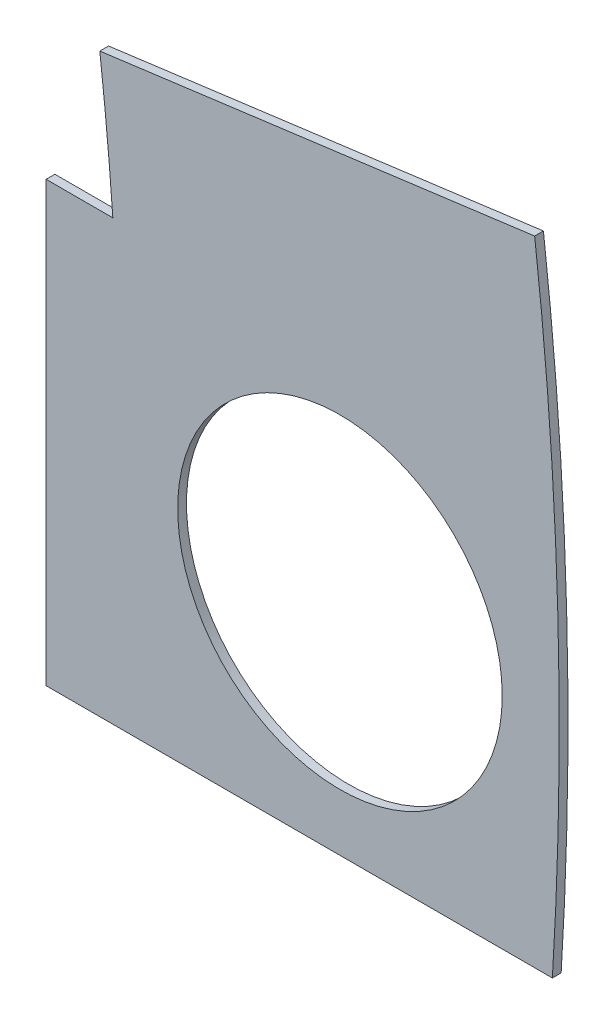
SolidWorks part; units mm, degrees
material "Copper"
ref_plane "Front Plane" through (0, 0, 0) normal (0, 0, 1) x (1, 0, 0)
ref_plane "Top Plane" through (0, 0, 0) normal (0, 1, 0) x (1, 0, 0)
ref_plane "Right Plane" through (0, 0, 0) normal (1, 0, 0) x (0, 0, -1)
sketch "Sketch1" plane through (0, 0, 0) normal (0, 0, 1) x (1, 0, 0)
  line L0 (0, 0) -> (320.3893, 0) construction
  line L1 (0, 0) -> (155.5285, 155.5285) construction
  line L2 (67.2115, 76.1917) -> (8.6967, 17.6769)
  line L3 (8.6967, 17.6769) -> (7.229, 14.1336)
  line L4 (101.4014, -6.35) -> (18.6489, -6.35)
  line L5 (15.1056, -4.8823) -> (18.6489, -6.35)
  line L6 (88.6729, 6.35) -> (27.8605, 6.35)
  line L9 (67.1914, 58.2111) -> (24.1905, 15.2102)
  line L10 (0, 0) -> (40.4486, 97.6516) construction
  line L11 (0, 0) -> (123.4567, -51.1374) construction
  line L18 (8.6967, 17.6769) -> (13.294, 8.6183) construction
  line L19 (18.6489, -6.35) -> (15.4943, 3.3063) construction
  line L20 (27.8605, 6.35) -> (27.7442, 6.7059) construction
  line L21 (24.1905, 15.2102) -> (24.3599, 14.8764) construction
  arc A0 (7.229, 14.1336) -> (15.1056, -4.8823) centre (0, 0) cw
  arc A1 (67.2115, 76.1917) -> (101.4014, -6.35) centre (0, 0) cw
  arc A2 (24.1905, 15.2102) -> (27.8605, 6.35) centre (0, 0) cw
  arc A3 (67.1914, 58.2111) -> (88.6729, 6.35) centre (0, 0) cw
  arc A8 (13.294, 8.6183) -> (15.4943, 3.3063) centre (0, 0) cw construction
  arc A9 (24.3599, 14.8764) -> (27.7442, 6.7059) centre (0, 0) cw construction
  dimension "D1" = 45
  dimension "D3" = 6.35
  dimension "D4" = 15.875
  dimension "D7" = 22.5
  dimension "D8" = 101.6
  dimension "D11" = 12.7
  dimension "D12" = 12.7
  dimension "D2" = 6.35
  dimension "D5" = 67.5
  dimension "D9" = 1.27
  dimension "D10" = 1.27
  dimension "D6" = 12.7
extrude "Boss-Extrude1" add sketch "Sketch1" along normal blind 0.254
sketch "Sketch2" plane through (0, 0, 0.254) normal (0, 0, 1) x (1, 0, 0)
  line L0 (0, 0) -> (101.6, 0) construction
  line L1 (0, 0) -> (71.842, 71.842) construction
  line L3 (0, 0) -> (22.225, 0) construction
  line L4 (0, 0) -> (15.7154, 15.7154) construction
  line L5 (0, 0) -> (95.25, 0) construction
  line L6 (0, 0) -> (92.0044, 24.6525) construction
  arc A0 (101.4014, -6.35) -> (67.2115, 76.1917) centre (0, 0) ccw construction
  circle A1 centre (22.225, 0) radius 4.699
  arc A2 (15.1056, -4.8823) -> (7.229, 14.1336) centre (0, 0) ccw construction
  circle A3 centre (36.195, 0) radius 4.699
  circle A4 centre (61.722, 0) radius 4.699
  circle A5 centre (75.692, 0) radius 4.699
  circle A6 centre (95.25, 0) radius 4.699
  circle A7 centre (15.7154, 15.7154) radius 4.699
  circle A8 centre (25.5937, 25.5937) radius 4.699
  circle A9 centre (43.644, 43.644) radius 4.699
  circle A10 centre (53.5223, 53.5223) radius 4.699
  circle A11 centre (92.0044, 24.6525) radius 4.699
  circle A12 centre (82.4889, 47.625) radius 4.699
  circle A13 centre (67.3519, 67.3519) radius 4.699
  dimension "D3" = 9.398
  dimension "D1" = 45
  dimension "D2" = 6.35
  dimension "D4" = 6.35
  dimension "D5" = 13.97
  dimension "D7" = 13.97
  dimension "D8" = 19.558
  dimension "D9" = 45
  dimension "D10" = 15
  dimension "D11" = 25.527
  dimension "D6" = 2
extrude "Cut-Extrude1" cut sketch "Sketch2" against normal through all
sketch "Sketch3" plane through (0, 0, 0.254) normal (0, 0, 1) x (1, 0, 0)
  line L0 (15.2664, 24.2467) -> (17.0625, 26.0427)
  line L1 (15.2664, 24.2467) -> (15.7154, 23.7977)
  line L2 (17.0625, 26.0427) -> (17.5115, 25.5937)
  line L3 (15.7154, 23.7977) -> (17.5115, 25.5937)
  line L4 (67.2115, 76.1917) -> (8.6967, 17.6769) construction
  line L5 (44.9911, 53.9713) -> (43.195, 52.1753)
  line L6 (44.9911, 53.9713) -> (45.4401, 53.5223)
  line L7 (43.195, 52.1753) -> (43.644, 51.7263)
  line L8 (45.4401, 53.5223) -> (43.644, 51.7263)
  line L9 (27.94, -6.35) -> (30.48, -6.35)
  line L10 (27.94, -6.35) -> (27.94, -5.715)
  line L11 (30.48, -6.35) -> (30.48, -5.715)
  line L12 (27.94, -5.715) -> (30.48, -5.715)
  line L13 (18.6489, -6.35) -> (101.4014, -6.35) construction
  line L14 (67.437, -6.35) -> (69.977, -6.35)
  line L15 (67.437, -6.35) -> (67.437, -5.715)
  line L16 (69.977, -6.35) -> (69.977, -5.715)
  line L17 (67.437, -5.715) -> (69.977, -5.715)
  line L18 (29.2307, 38.211) -> (31.0268, 40.007)
  line L19 (29.2307, 38.211) -> (29.6797, 37.762)
  line L20 (31.0268, 40.007) -> (31.4758, 39.558)
  line L21 (29.6797, 37.762) -> (31.4758, 39.558)
  line L22 (56.845, 65.8253) -> (55.049, 64.0292)
  line L23 (56.845, 65.8253) -> (57.294, 65.3763)
  line L24 (55.049, 64.0292) -> (55.498, 63.5802)
  line L25 (57.294, 65.3763) -> (55.498, 63.5802)
  line L26 (47.6885, -6.35) -> (50.2285, -6.35)
  line L27 (47.6885, -6.35) -> (47.6885, -5.715)
  line L28 (50.2285, -6.35) -> (50.2285, -5.715)
  line L29 (47.6885, -5.715) -> (50.2285, -5.715)
  line L30 (84.201, -6.35) -> (86.741, -6.35)
  line L31 (84.201, -6.35) -> (84.201, -5.715)
  line L32 (86.741, -6.35) -> (86.741, -5.715)
  line L33 (84.201, -5.715) -> (86.741, -5.715)
  line L34 (0, 0) -> (100.7308, 13.2615) construction
  line L35 (0, 0) -> (93.8662, 38.8806) construction
  line L36 (0, 0) -> (80.6047, 61.8502) construction
  line L37 (0, 0) -> (101.6, 0) construction
  line L38 (99.9355, 14.4377) -> (100.267, 11.9194)
  line L39 (99.9355, 14.4377) -> (101.1946, 14.6035)
  line L40 (100.267, 11.9194) -> (101.5261, 12.0852)
  line L41 (101.1946, 14.6035) -> (101.5261, 12.0852)
  line L42 (99.9355, 14.4377) -> (101.5261, 12.0852) construction
  line L43 (100.267, 11.9194) -> (101.1946, 14.6035) construction
  line L44 (93.7655, 37.4643) -> (94.9388, 37.9503)
  line L45 (93.7655, 37.4643) -> (92.7935, 39.811)
  line L46 (94.9388, 37.9503) -> (93.9668, 40.297)
  line L47 (92.7935, 39.811) -> (93.9668, 40.297)
  line L48 (93.7655, 37.4643) -> (93.9668, 40.297) construction
  line L49 (94.9388, 37.9503) -> (92.7935, 39.811) construction
  line L50 (79.3278, 62.4712) -> (80.874, 60.456)
  line L51 (79.3278, 62.4712) -> (80.3354, 63.2443)
  line L52 (80.874, 60.456) -> (81.8816, 61.2292)
  line L53 (80.3354, 63.2443) -> (81.8816, 61.2292)
  line L54 (79.3278, 62.4712) -> (81.8816, 61.2292) construction
  line L55 (80.874, 60.456) -> (80.3354, 63.2443) construction
  line L56 (13.5939, 7.0054) -> (14.5659, 4.6588)
  line L57 (13.5939, 7.0054) -> (14.7672, 7.4914)
  line L58 (14.5659, 4.6588) -> (15.7393, 5.1448)
  line L59 (14.7672, 7.4914) -> (15.7393, 5.1448)
  line L60 (13.5939, 7.0054) -> (15.7393, 5.1448) construction
  line L61 (14.5659, 4.6588) -> (14.7672, 7.4914) construction
  circle A0 centre (15.7154, 15.7154) radius 4.699 construction
  circle A1 centre (43.644, 43.644) radius 4.699 construction
  circle A2 centre (22.225, 0) radius 4.699 construction
  circle A3 centre (61.722, 0) radius 4.699 construction
  arc A4 (101.4014, -6.35) -> (67.2115, 76.1917) centre (0, 0) ccw construction
  arc A9 (15.1056, -4.8823) -> (7.229, 14.1336) centre (0, 0) ccw construction
  circle A10 centre (36.195, 0) radius 4.699 construction
  circle A11 centre (75.692, 0) radius 4.699 construction
  circle A12 centre (25.5937, 25.5937) radius 4.699 construction
  circle A13 centre (53.5223, 53.5223) radius 4.699 construction
  point P75 (14.6666, 6.0751)
  dimension "D2" = 5.715
  dimension "D3" = 2.54
  dimension "D6" = 5.715
  dimension "D8" = 0.635
  dimension "D9" = 5.715
  dimension "D12" = 5.715
  dimension "D4" = 7.5
  dimension "D5" = 22.5
  dimension "D7" = 37.5
  dimension "D10" = 90
  dimension "D11" = 1.27
  dimension "D14" = 0.635
  dimension "D15" = 90
  dimension "D18" = 0.635
  dimension "D19" = 90
  dimension "D22" = 0.635
  dimension "D20" = 1.27
  dimension "D17" = 0.635
  dimension "D13" = 11.4935
  dimension "D16" = 8.509
  dimension "D21" = 11.4935
  dimension "D23" = 8.509
extrude "Cut-Extrude2" cut sketch "Sketch3" against normal through all
sketch "Sketch5" plane through (0, 0, 0.254) normal (0, 0, 1) x (1, 0, 0)
  line L1 (86.741, -7.62) -> (86.741, 10.1387)
  line L2 (86.741, 10.1387) -> (102.87, 12.2621)
  line L3 (84.201, -5.715) -> (84.201, -6.35) construction
  line L4 (102.87, 12.2621) -> (102.87, -7.62)
  line L5 (102.87, -7.62) -> (86.741, -7.62)
  line L6 (100.5572, 14.5196) -> (99.9355, 14.4377) construction
  line L10 (86.741, -6.35) -> (101.4014, -6.35) construction
  arc A0 (101.4014, -6.35) -> (100.8887, 12.0013) centre (0, 0) ccw construction
  dimension "D1" = 2.54
  dimension "D2" = 2.54
  dimension "D3" = 1.27
  dimension "D4" = 1.27
  dimension "D5" = 90
extrude "Cut-Extrude5" cut sketch "Sketch5" against normal through all flip side to cut
equation "\"cSep\"= 1.005"
equation "\"D11@Sketch2\"=\"cSep\""
equation "\"cSep2\"= \"D8@Sketch2\""
equation "\"D13@Sketch3\"=\"cSep\"/2-.05"
equation "\"D16@Sketch3\"=\"cSep2\"/2-.05"
equation "\"D21@Sketch3\"=\"cSep\"/2-.05"
equation "\"D23@Sketch3\"=\"cSep2\"/2-.05"
